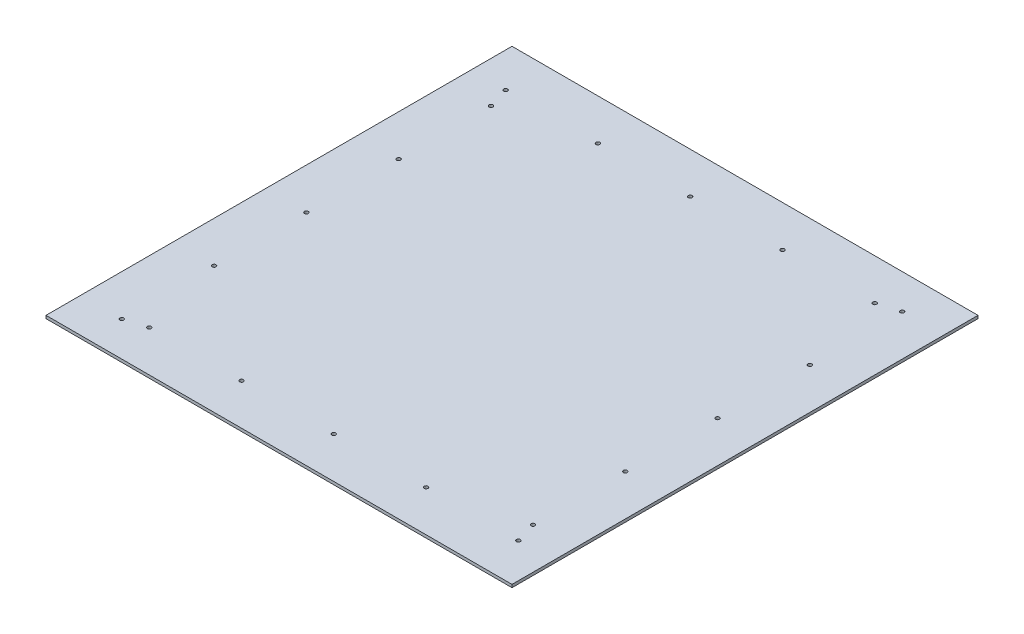
SolidWorks part; units mm, degrees
material "6061 Alloy"
ref_plane "Front Plane" through (0, 0, 0) normal (0, 0, 1) x (1, 0, 0)
ref_plane "Top Plane" through (0, 0, 0) normal (0, 1, 0) x (1, 0, 0)
ref_plane "Right Plane" through (0, 0, 0) normal (1, 0, 0) x (0, 0, -1)
sketch "Sketch1" plane through (0, 0, 0) normal (0, 1, 0) x (1, 0, 0)
  line L1 (-255, -255) -> (255, -255)
  line L2 (-255, -255) -> (-255, 255)
  line L3 (-255, 255) -> (255, 255)
  line L4 (255, -255) -> (255, 255)
  line L5 (-255, -255) -> (255, 255) construction
  line L6 (-255, 255) -> (255, -255) construction
  point P0 (0, 0)
  dimension "D1" = 510
  dimension "D2" = 510
extrude "Boss-Extrude1" add sketch "Sketch1" along normal blind 3.175
sketch "Sketch3" plane through (0, 0, 0) normal (0, -1, 0) x (1, 0, 0)
  line L1 (225, -225) -> (-225, -225) construction
  line L2 (225, -225) -> (225, 225) construction
  line L3 (225, 225) -> (-225, 225) construction
  line L4 (-225, -225) -> (-225, 225) construction
  line L5 (225, -225) -> (-225, 225) construction
  line L6 (225, 225) -> (-225, -225) construction
  line L7 (-255, 255) -> (255, -255) construction
  line L8 (210, 210) -> (-210, 210) construction
  line L9 (-210, -210) -> (-210, 210) construction
  line L10 (210, -210) -> (-210, -210) construction
  line L11 (210, -210) -> (210, 210) construction
  circle A0 centre (217, 210) radius 2.1
  circle A1 centre (116, 210) radius 2.1
  circle A2 centre (15, 210) radius 2.1
  circle A3 centre (-86, 210) radius 2.1
  circle A4 centre (-187, 210) radius 2.1
  circle A5 centre (-210, 217) radius 2.1
  circle A6 centre (-210, 116) radius 2.1
  circle A7 centre (-210, 15) radius 2.1
  circle A8 centre (-210, -86) radius 2.1
  circle A9 centre (-210, -187) radius 2.1
  circle A10 centre (-217, -210) radius 2.1
  circle A11 centre (-116, -210) radius 2.1
  circle A12 centre (-15, -210) radius 2.1
  circle A13 centre (86, -210) radius 2.1
  circle A14 centre (187, -210) radius 2.1
  circle A15 centre (210, -217) radius 2.1
  circle A16 centre (210, -116) radius 2.1
  circle A17 centre (210, -15) radius 2.1
  circle A18 centre (210, 86) radius 2.1
  circle A19 centre (210, 187) radius 2.1
  point P0 (0, 0)
  dimension "D1" = 450
  dimension "D5" = 5
  dimension "D2" = 8
  dimension "D4" = 8
  dimension "D6" = 8
  dimension "D8" = 8
  dimension "D3" = 5
  dimension "D7" = 5
  dimension "D9" = 5
extrude "Cut-Extrude1" cut sketch "Sketch3" against normal through all
